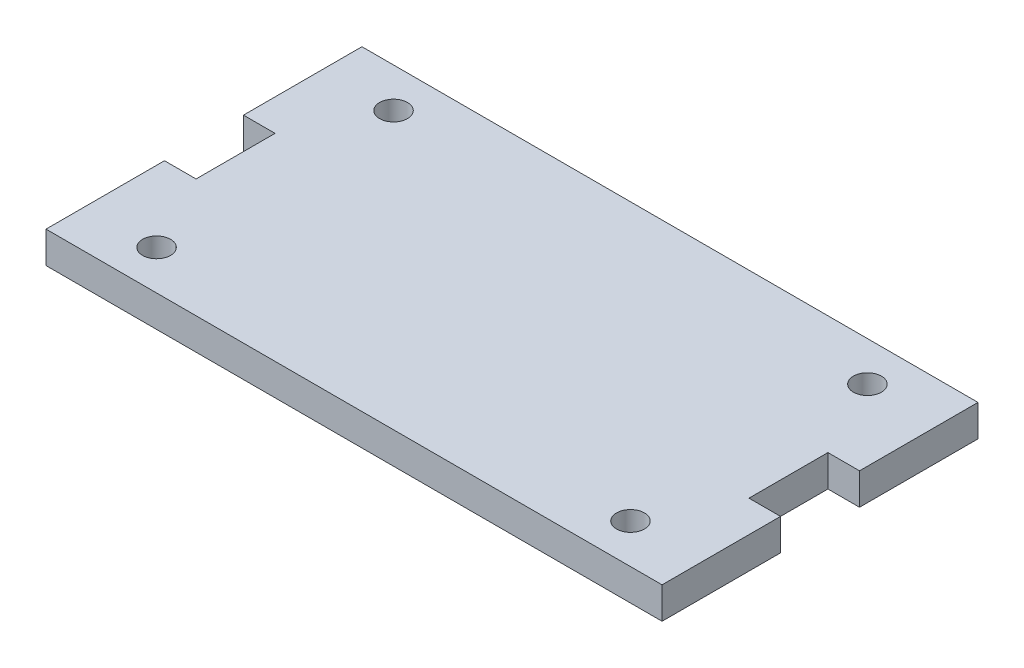
SolidWorks part; units mm, degrees
ref_plane "Front Plane" through (0, 0, 0) normal (0, 0, 1) x (1, 0, 0)
ref_plane "Top Plane" through (0, 0, 0) normal (0, 1, 0) x (1, 0, 0)
ref_plane "Right Plane" through (0, 0, 0) normal (1, 0, 0) x (0, 0, -1)
sketch "Sketch1" plane through (0, 0, 0) normal (0, 1, 0) x (1, 0, 0)
  line L1 (-44.45, 25.4) -> (44.45, 25.4)
  line L2 (-44.45, 25.4) -> (-44.45, -25.4)
  line L3 (-44.45, -25.4) -> (44.45, -25.4)
  line L4 (44.45, 25.4) -> (44.45, -25.4)
  line L5 (-44.45, 25.4) -> (44.45, -25.4) construction
  line L6 (-44.45, -25.4) -> (44.45, 25.4) construction
  line L7 (-44.45, 25.4) -> (-49.53, 25.4)
  line L8 (-44.45, 25.4) -> (-44.45, 6.35)
  line L9 (-44.45, 6.35) -> (-49.53, 6.35)
  line L10 (-49.53, 25.4) -> (-49.53, 6.35)
  line L11 (-44.45, -25.4) -> (-49.53, -25.4)
  line L12 (-44.45, -25.4) -> (-44.45, -6.35)
  line L13 (-44.45, -6.35) -> (-49.53, -6.35)
  line L14 (-49.53, -25.4) -> (-49.53, -6.35)
  line L15 (44.45, 25.4) -> (49.53, 25.4)
  line L16 (44.45, 25.4) -> (44.45, 6.35)
  line L17 (44.45, 6.35) -> (49.53, 6.35)
  line L18 (49.53, 25.4) -> (49.53, 6.35)
  line L19 (44.45, -25.4) -> (49.53, -25.4)
  line L20 (44.45, -25.4) -> (44.45, -6.35)
  line L21 (44.45, -6.35) -> (49.53, -6.35)
  line L22 (49.53, -25.4) -> (49.53, -6.35)
  point P0 (0, 0)
  dimension "D1" = 88.9
  dimension "D2" = 50.8
  dimension "D3" = 5.08
  dimension "D4" = 12.7
extrude "Boss-Extrude1" add sketch "Sketch1" along normal blind 5.08 contours L4 L1 L2 L3 | L7 L10 L9 L2 | L14 L11 L2 L13 | L19 L22 L21 L4 | L18 L15 L4 L17
hole_wizard "#8 Clearance Hole1" positions "Sketch2" profile "Sketch3" hole size "#8" standard "ANSI Inch" end condition through all
sketch "Sketch2" plane through (0, 5.08, 0) normal (0, 1, 0) x (1, 0, 0)
  line L1 (38.1, -19.05) -> (-38.1, -19.05)
  line L2 (38.1, -19.05) -> (38.1, 19.05)
  line L3 (38.1, 19.05) -> (-38.1, 19.05)
  line L4 (-38.1, -19.05) -> (-38.1, 19.05)
  line L5 (38.1, -19.05) -> (-38.1, 19.05) construction
  line L6 (38.1, 19.05) -> (-38.1, -19.05) construction
  point P2 (-38.1, 19.05)
  point P9 (38.1, -19.05)
  point P10 (38.1, 19.05)
  point P11 (-38.1, -19.05)
  point P16 (0, 0)
  dimension "D1" = 76.2
  dimension "D2" = 38.1
sketch "Sketch3" plane through (-38.1, 5.08, -19.05) normal (1, 0, 0) x (0, 0, 1)
  line L0 (0, 0) -> (0, 5.08)
  line L1 (0, 5.08) -> (2.2479, 5.08)
  line L2 (2.2479, 5.08) -> (2.2479, 0)
  line L5 (2.2479, 0) -> (0, 0)
  line L11 (0, -6.35) -> (0, 107.95) construction
  dimension "Thru Hole Dia." = 4.4958
  dimension "Thru Hole Depth" = 5.08
